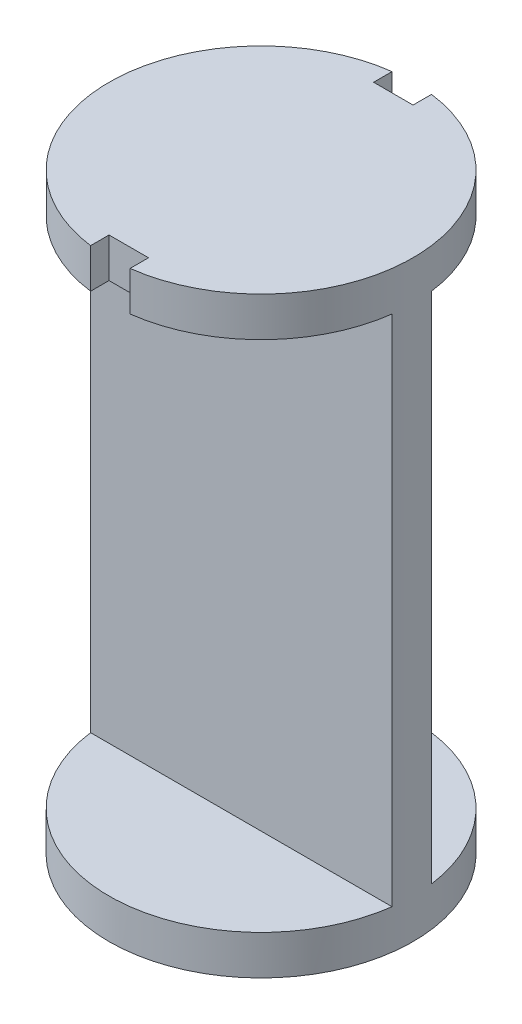
SolidWorks part; units mm, degrees
material "Balsa"
ref_plane "Front Plane" through (0, 0, 0) normal (0, 0, 1) x (1, 0, 0)
ref_plane "Top Plane" through (0, 0, 0) normal (0, 1, 0) x (1, 0, 0)
ref_plane "Right Plane" through (0, 0, 0) normal (1, 0, 0) x (0, 0, -1)
sketch "Sketch1" plane through (0, 0, 0) normal (0, 1, 0) x (1, 0, 0)
  circle A0 centre (0, 0) radius 38.5
  dimension "D1" = 77
extrude "Boss-Extrude1" add sketch "Sketch1" along normal blind 10
ref_plane "Plane1" through (0, 150, 0) normal (0, 1, 0) x (1, 0, 0)
sketch "Sketch2" plane through (0, 150, 0) normal (0, 1, 0) x (1, 0, 0)
  circle A0 centre (0, 0) radius 38.5 construction
  circle A1 centre (0, 0) radius 38.5
extrude "Boss-Extrude2" add sketch "Sketch2" against normal blind 10 separate body
sketch "Sketch3" plane through (0, 10, 0) normal (0, 1, 0) x (1, 0, 0)
  line L1 (38.1739, 5) -> (-38.1739, 5)
  line L3 (38.1739, -5) -> (-38.1739, -5)
  line L5 (38.1739, 5) -> (-38.1739, -5) construction
  line L6 (38.1739, -5) -> (-38.1739, 5) construction
  circle A0 centre (0, 0) radius 38.5 construction
  arc A1 (-38.1739, 5) -> (-38.1739, -5) centre (0, 0) ccw
  arc A2 (38.1739, -5) -> (38.1739, 5) centre (0, 0) ccw
  point P0 (0, 0)
  dimension "D1" = 10
extrude "Boss-Extrude3" add sketch "Sketch3" along normal up to next (140 mm away)
sketch "Sketch4" plane through (0, 150, 0) normal (0, 1, 0) x (1, 0, 0)
  line L0 (0, 0) -> (7.5059, 0) construction
  line L1 (5, 43.5) -> (-5, 43.5)
  line L2 (5, 43.5) -> (5, 33.5)
  line L3 (5, 33.5) -> (-5, 33.5)
  line L4 (-5, 43.5) -> (-5, 33.5)
  line L5 (5, 43.5) -> (-5, 33.5) construction
  line L6 (5, 33.5) -> (-5, 43.5) construction
  line L7 (5, -33.5) -> (-5, -33.5)
  line L8 (-5, -43.5) -> (-5, -33.5)
  line L9 (5, -43.5) -> (-5, -43.5)
  line L10 (5, -43.5) -> (5, -33.5)
  circle A0 centre (0, 0) radius 38.5 construction
  point P0 (0, 38.5)
  dimension "D1" = 10
  dimension "D2" = 10
extrude "Cut-Extrude1" cut sketch "Sketch4" against normal up to next
equation "\"diamfuselaje int\"=77"
equation "\"D1@Sketch1\"=\"diamfuselaje int\""
